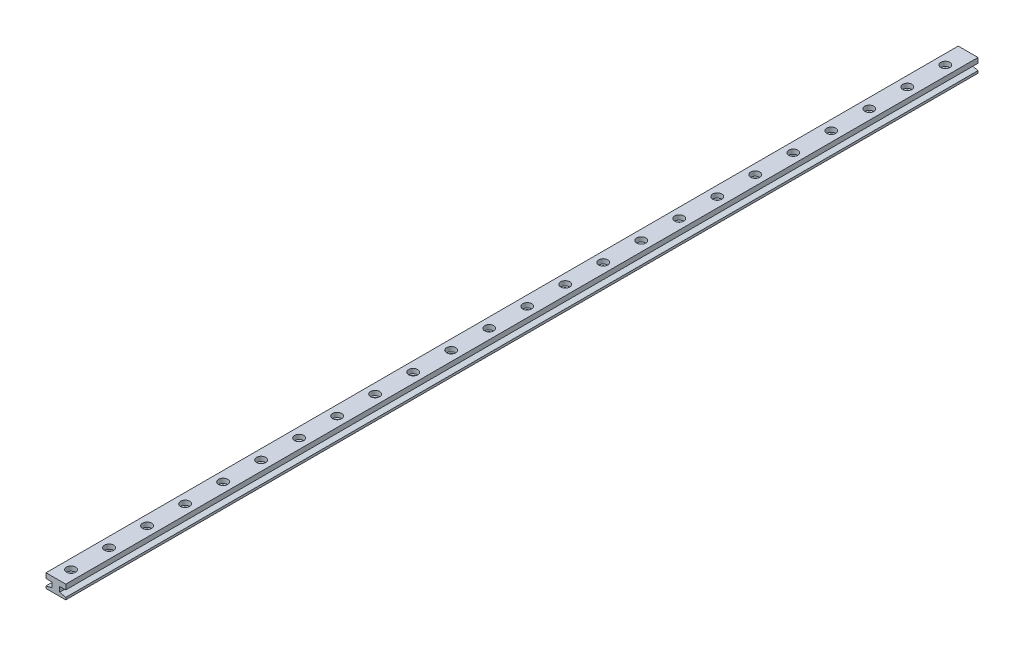
SolidWorks part; units mm, degrees
ref_plane "前视基准面" through (0, 0, 0) normal (0, 0, 1) x (1, 0, 0)
ref_plane "上视基准面" through (0, 0, 0) normal (0, 1, 0) x (1, 0, 0)
ref_plane "右视基准面" through (0, 0, 0) normal (1, 0, 0) x (0, 0, -1)
sketch "草图1" plane through (0, 0, 0) normal (0, 0, 1) x (1, 0, 0)
  line L0 (0, 6.4911) -> (0, -7.1696) construction
  line L1 (-6.5, 4.5) -> (6.5, 4.5)
  line L2 (-6.5, 4.5) -> (-6.5, 1.2)
  line L3 (-6.5, -4.5) -> (6.5, -4.5)
  line L4 (6.5, 4.5) -> (6.5, 1.2)
  line L5 (-6.5, 4.5) -> (6.5, -4.5) construction
  line L6 (-6.5, -4.5) -> (6.5, 4.5) construction
  line L7 (6.5, 1.2) -> (2.5, 1.2)
  line L8 (2.5, 1.2) -> (2.5, -2.0765)
  line L9 (2.5, -2.0765) -> (6.5, -3)
  line L10 (6.5, -3) -> (6.5, -4.5)
  line L11 (-2.5, -2.0765) -> (-6.5, -3)
  line L12 (-2.5, 1.2) -> (-2.5, -2.0765)
  line L13 (-6.5, 1.2) -> (-2.5, 1.2)
  line L14 (-6.5, -3) -> (-6.5, -4.5)
  point P0 (0, 0)
  dimension "D1" = 13
  dimension "D2" = 9
  dimension "D3" = 3.3
  dimension "D4" = 2.5
  dimension "D5" = 1.5
  dimension "D6" = 13
extrude "凸台-拉伸1" add sketch "草图1" along normal blind 600
sketch "草图2" plane through (0, 4.5, 0) normal (0, 1, 0) x (1, 0, 0)
  line L0 (0, -600) -> (0, -477.7695) construction
  line L1 (6.5, -600) -> (-6.5, -600) construction
  circle A0 centre (0, -590) radius 3
  dimension "D1" = 10
  dimension "D2" = 6
extrude "切除-拉伸1" cut sketch "草图2" against normal blind 3
sketch "草图3" plane through (0, 1.5, 0) normal (0, 1, 0) x (1, 0, 0)
  circle A0 centre (0, -590) radius 1.6
  dimension "D1" = 3.2
extrude "切除-拉伸2" cut sketch "草图3" against normal up to next (6 mm away)
pattern_linear "阵列(线性)1" count 24 spacing 25 along (0, 0, -1) of "切除-拉伸2", "切除-拉伸1"
